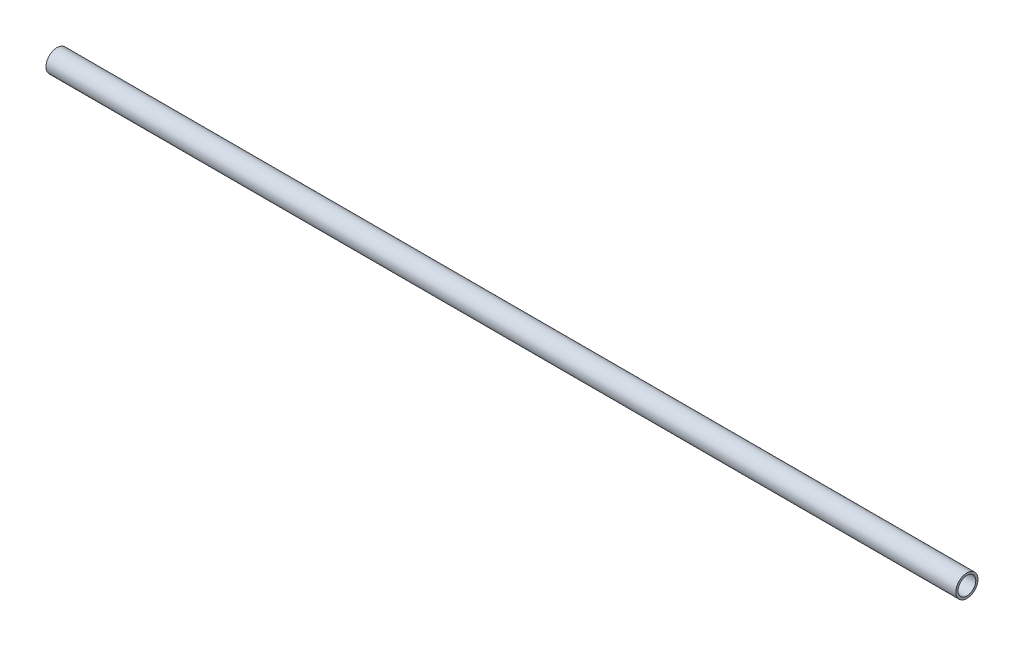
SolidWorks part; units mm, degrees
ref_plane "前视基准面" through (0, 0, 0) normal (0, 0, 1) x (1, 0, 0)
ref_plane "上视基准面" through (0, 0, 0) normal (0, 1, 0) x (1, 0, 0)
ref_plane "右视基准面" through (0, 0, 0) normal (1, 0, 0) x (0, 0, -1)
sketch "草图1" plane through (0, 0, 0) normal (1, 0, 0) x (0, 0, -1)
  circle A0 centre (0, 0) radius 4
  circle A1 centre (0, 0) radius 5
  dimension "D1" = 8
  dimension "D2" = 10
extrude "凸台-拉伸1" add sketch "草图1" along normal blind 410
